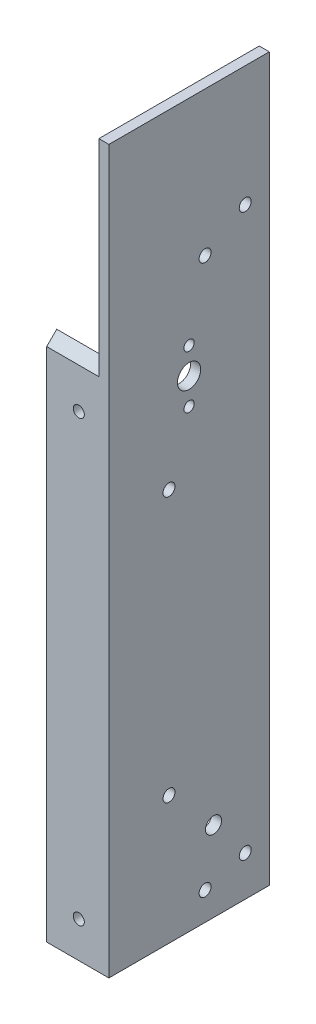
SolidWorks part; units mm, degrees
ref_plane "Front Plane" through (0, 0, 0) normal (0, 0, 1) x (1, 0, 0)
ref_plane "Top Plane" through (0, 0, 0) normal (0, 1, 0) x (1, 0, 0)
ref_plane "Right Plane" through (0, 0, 0) normal (1, 0, 0) x (0, 0, -1)
sketch "Sketch1" plane through (0, 0, 0) normal (0, 1, 0) x (1, 0, 0)
  line L0 (0, 0) -> (-19.685, 0)
  line L1 (-19.685, 0) -> (-19.685, 3.175)
  line L2 (-19.685, 3.175) -> (-3.175, 3.175)
  line L3 (-3.175, 3.175) -> (-3.175, 50.8)
  line L4 (-3.175, 50.8) -> (0, 50.8)
  line L5 (0, 50.8) -> (0, 0)
  dimension "D1" = 3.175
  dimension "D2" = 16.51
  dimension "D3" = 50.8
extrude "Boss-Extrude1" add sketch "Sketch1" along normal blind 203.2 contours L2 L3 L4 L5 L0 L1
sketch "Sketch2" plane through (0, 0, 0) normal (1, 0, 0) x (0, 0, -1)
  line L2 (50.8, 203.2) -> (0, 203.2) construction
  line L4 (0, 142.9065) -> (-14.0217, 144.6224)
  line L5 (-14.0217, 144.6224) -> (-5.0458, 217.9697)
  line L6 (-5.0458, 217.9697) -> (74.5137, 222.3899)
  line L7 (74.5137, 222.3899) -> (74.5137, 203.2)
  line L8 (0, 142.9065) -> (49.3603, 182.8469)
  line L9 (0, 203.2) -> (0, 0) construction
  line L10 (49.3603, 182.8469) -> (50.7689, 183.9867)
  line L11 (50.7689, 183.9867) -> (74.5137, 203.2)
sketch "Sketch5" plane through (-3.175, 0, 0) normal (-1, 0, 0) x (0, 0, 1)
  line L0 (0, 163.322) -> (-50.8, 214.122)
  line L1 (-50.8, 203.2) -> (-50.8, 0) construction
  line L2 (0, 203.2) -> (0, 0) construction
  line L3 (0, 163.322) -> (33.1966, 163.322)
  line L4 (33.1966, 163.322) -> (33.1966, 256.0472)
  line L5 (33.1966, 256.0472) -> (-60.8232, 256.0472)
  line L6 (-60.8232, 256.0472) -> (-60.8232, 214.122)
  line L7 (-60.8232, 214.122) -> (-50.8, 214.122)
  dimension "D1" = 163.322
  dimension "D2" = 135
extrude "Cut-Extrude3" cut sketch "Sketch5" against normal through all and the other way through all
ref_plane "Plane1" through (0, 0, -50.8) normal (0, 0, 1) x (1, 0, 0)
sketch "Sketch7" plane through (0, 0, 0) normal (1, 0, 0) x (0, 0, -1)
  line L0 (25.4, 144.018) -> (25.4, 160.782) construction
  line L1 (0, 152.4) -> (50.8, 152.4) construction
  line L2 (0, 163.322) -> (0, 0) construction
  line L3 (50.8, 203.2) -> (50.8, 0) construction
  line L4 (50.8, 0) -> (0, 0) construction
  circle A0 centre (25.4, 152.4) radius 3.683
  circle A1 centre (25.4, 160.782) radius 1.632
  circle A2 centre (25.4, 144.018) radius 1.632
  point P6 (25.4, 152.4)
  point P13 (25.4, 152.4)
  dimension "D1" = 7.366
  dimension "D3" = 3.2639
  dimension "D2" = 16.764
  dimension "D4" = 152.4
extrude "Cut-Extrude4" cut sketch "Sketch7" against normal through all
sketch "Sketch8" plane through (-3.175, 0, 0) normal (-1, 0, 0) x (0, 0, 1)
  circle A0 centre (-30.48, 182.88) radius 1.8987
  circle A1 centre (-30.48, 182.88) radius 1.7526 construction
  circle A2 centre (-30.48, 8.89) radius 1.8986
  circle A3 centre (-30.48, 8.89) radius 1.7526 construction
  dimension "D1" = 3.7973
  dimension "D2" = 3.7973
extrude "Cut-Extrude5" cut sketch "Sketch8" against normal through all
sketch "Sketch9" plane through (-3.175, 0, 0) normal (-1, 0, 0) x (0, 0, 1)
  line L0 (-50.8, 0) -> (0, 0) construction
  line L1 (0, 163.322) -> (0, 0) construction
  circle A0 centre (-19.05, 40.5773) radius 1.8986
  circle A1 centre (-19.05, 124.3973) radius 1.8986
  dimension "D1" = 3.7973
  dimension "D2" = 40.5773
  dimension "D3" = 19.05
  dimension "D4" = 83.82
extrude "Cut-Extrude6" cut sketch "Sketch9" against normal through all
sketch "Sketch10" plane through (0, 0, -3.175) normal (0, 0, -1) x (-1, 0, 0)
  circle A0 centre (9.525, 11.43) radius 1.7526
  circle A1 centre (9.525, 150.6039) radius 1.7526
  dimension "D1" = 3.5052
extrude "Cut-Extrude7" cut sketch "Sketch10" against normal through all
sketch "Sketch11" plane through (0, 0, 0) normal (1, 0, 0) x (0, 0, -1)
  line L0 (0, 228.6) -> (0, 163.322)
  line L1 (50.8, 203.2) -> (39.878, 203.2)
  line L2 (50.8, 203.2) -> (50.8, 228.6)
  line L3 (50.8, 228.6) -> (0, 228.6)
  line L6 (0, 163.322) -> (39.878, 203.2)
  dimension "D1" = 25.4
extrude "Boss-Extrude2" add sketch "Sketch11" against normal blind 3.175
sketch "Sketch12" plane through (-3.175, 0, 0) normal (-1, 0, 0) x (0, 0, 1)
  circle A0 centre (-33.1362, 25.4) radius 2.54
extrude "Cut-Extrude8" cut sketch "Sketch12" against normal through all
sketch "Sketch13" plane through (-3.175, 0, 0) normal (-1, 0, 0) x (0, 0, 1)
  circle A0 centre (-43.18, 12.7) radius 1.8986
  circle A1 centre (-43.18, 190.4989) radius 1.8986
extrude "Cut-Extrude9" cut sketch "Sketch13" against normal through all
